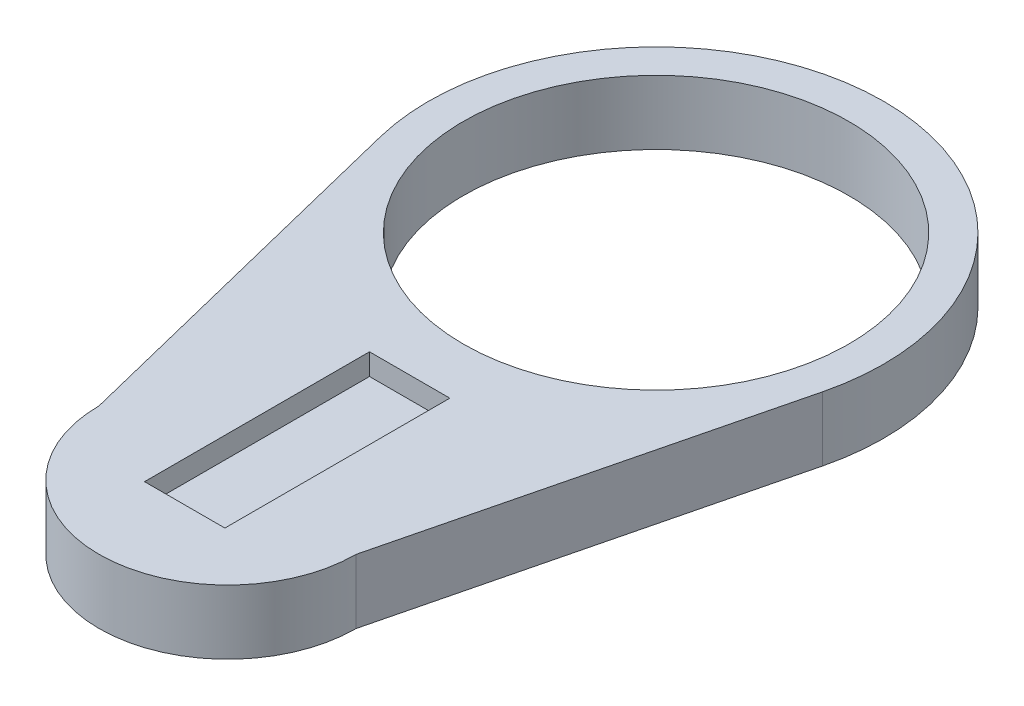
SolidWorks part; units mm, degrees
ref_plane "Front Plane" through (0, 0, 0) normal (0, 0, 1) x (1, 0, 0)
ref_plane "Top Plane" through (0, 0, 0) normal (0, 1, 0) x (1, 0, 0)
ref_plane "Right Plane" through (0, 0, 0) normal (1, 0, 0) x (0, 0, -1)
sketch "Sketch1" plane through (0, 0, 0) normal (0, 1, 0) x (1, 0, 0)
  line L0 (-20.6288, 34.8996) -> (-12, 0)
  line L1 (0, 120.2958) -> (0, -44.3308) construction
  line L2 (20.6288, 34.8996) -> (12, 0)
  arc A0 (-12, 0) -> (12, 0) centre (0, 0) ccw
  circle A1 centre (0, 40) radius 18
  arc A2 (20.6288, 34.8996) -> (-20.6288, 34.8996) centre (0, 40) ccw
  dimension "D1" = 36
  dimension "D2" = 42.5
  dimension "D3" = 12
  dimension "D4" = 40
extrude "Boss-Extrude1" add sketch "Sketch1" along normal blind 6
sketch "Sketch2" plane through (0, 6, 0) normal (0, 1, 0) x (1, 0, 0)
  line L0 (0, 36.2798) -> (0, -14.4492) construction
  line L1 (-3.75, 17) -> (3.75, 17)
  line L2 (-3.75, 17) -> (-3.75, -4)
  line L3 (-3.75, -4) -> (3.75, -4)
  line L4 (3.75, 17) -> (3.75, -4)
  arc A0 (-12, 0) -> (12, 0) centre (0, 0) ccw construction
  arc A1 (-12, 0) -> (12, 0) centre (0, 0) ccw construction
  circle A2 centre (0, 40) radius 18 construction
  circle A3 centre (0, 40) radius 18 construction
  circle A5 centre (0, 0) radius 3.5 construction
  dimension "D3" = 7
  dimension "D4" = 0.5
  dimension "D1" = 7.5
  dimension "D2" = 21
extrude "Cut-Extrude1" cut sketch "Sketch2" against normal blind 2
